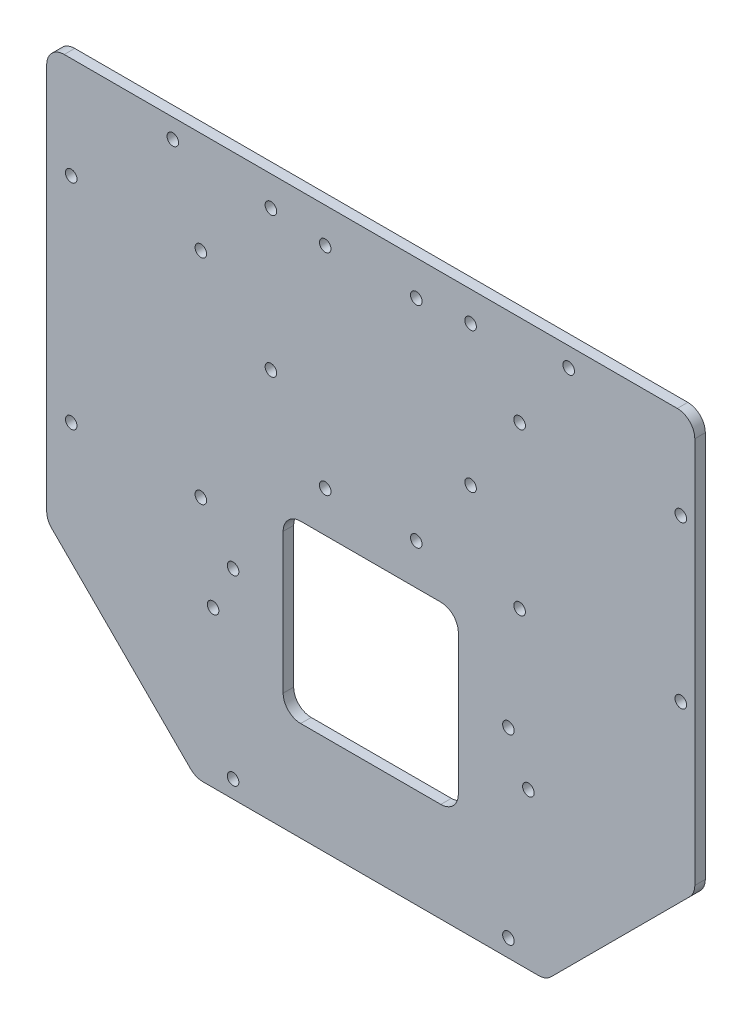
SolidWorks part; units mm, degrees
ref_plane "前视基准面" through (0, 0, 0) normal (0, 0, 1) x (1, 0, 0)
ref_plane "上视基准面" through (0, 0, 0) normal (0, 1, 0) x (1, 0, 0)
ref_plane "右视基准面" through (0, 0, 0) normal (1, 0, 0) x (0, 0, -1)
sketch "草图1" plane through (0, 0, 0) normal (0, 0, 1) x (1, 0, 0)
  line L1 (-87.5, 103.8596) -> (87.5, 103.8596)
  line L2 (-92.5, 98.8596) -> (-92.5, -13.6404)
  line L3 (-50, -56.1404) -> (50, -56.1404)
  line L4 (92.5, 98.8596) -> (92.5, -13.6404)
  line L5 (-92.5, 103.8596) -> (50, -56.1404) construction
  line L6 (-50, -56.1404) -> (92.5, 103.8596) construction
  line L7 (0, 103.8596) -> (0, -56.1404) construction
  line L9 (-92.5, -13.6404) -> (-50, -56.1404)
  line L10 (92.5, -13.6404) -> (50, -56.1404)
  arc A0 (87.5, 103.8596) -> (92.5, 98.8596) centre (87.5, 98.8596) cw
  arc A1 (-87.5, 103.8596) -> (-92.5, 98.8596) centre (-87.5, 98.8596) ccw
  point P0 (0, 0)
  dimension "D5" = 5
  dimension "D1" = 185
  dimension "D2" = 160
  dimension "D3" = 135
  dimension "D4" = 100
extrude "凸台-拉伸1" add sketch "草图1" along normal blind 3
sketch "草图2" plane through (0, 0, 3) normal (0, 0, 1) x (1, 0, 0)
  line L0 (87.5, 103.8596) -> (-87.5, 103.8596) construction
  line L1 (-28.5, 95.3596) -> (28.5, 95.3596) construction
  line L2 (-28.5, 95.3596) -> (-28.5, 55.3596) construction
  line L3 (-28.5, 55.3596) -> (28.5, 55.3596) construction
  line L4 (28.5, 95.3596) -> (28.5, 55.3596) construction
  line L5 (-28.5, 95.3596) -> (28.5, 55.3596) construction
  line L6 (-28.5, 55.3596) -> (28.5, 95.3596) construction
  line L7 (0, 0) -> (0, 75.3596) construction
  circle A0 centre (-28.5, 95.3596) radius 1.65
  circle A1 centre (28.5, 95.3596) radius 1.65
  circle A2 centre (-28.5, 55.3596) radius 1.65
  circle A3 centre (28.5, 55.3596) radius 1.65
  point P0 (0, 75.3596)
  dimension "D4" = 3.3
  dimension "D1" = 28.5
  dimension "D2" = 57
  dimension "D3" = 40
extrude "切除-拉伸1" cut sketch "草图2" against normal blind 10
sketch "草图3" plane through (0, 0, 3) normal (0, 0, 1) x (1, 0, 0)
  line L0 (-92.5, 98.8596) -> (-92.5, -13.6404) construction
  line L1 (-85.5, 74.8596) -> (-48.5, 74.8596) construction
  line L2 (-85.5, 74.8596) -> (-85.5, 13.8596) construction
  line L3 (-85.5, 13.8596) -> (-48.5, 13.8596) construction
  line L4 (-48.5, 74.8596) -> (-48.5, 13.8596) construction
  line L5 (-50, -56.1404) -> (50, -56.1404) construction
  circle A0 centre (-85.5, 74.8596) radius 1.65
  circle A1 centre (-48.5, 74.8596) radius 1.65
  circle A2 centre (-85.5, 13.8596) radius 1.65
  circle A3 centre (-48.5, 13.8596) radius 1.65
  dimension "D5" = 3.3
  dimension "D1" = 61
  dimension "D2" = 37
  dimension "D3" = 7
  dimension "D4" = 70
extrude "切除-拉伸2" cut sketch "草图3" against normal blind 10
sketch "草图4" plane through (0, 0, 3) normal (0, 0, 1) x (1, 0, 0)
  line L0 (92.5, -13.6404) -> (92.5, 98.8596) construction
  line L1 (42.5, 77.8596) -> (88.5, 77.8596) construction
  line L2 (42.5, 77.8596) -> (42.5, 31.8596) construction
  line L3 (42.5, 31.8596) -> (88.5, 31.8596) construction
  line L4 (88.5, 77.8596) -> (88.5, 31.8596) construction
  line L5 (87.5, 103.8596) -> (-87.5, 103.8596) construction
  circle A0 centre (42.5, 77.8596) radius 1.65
  circle A1 centre (88.5, 77.8596) radius 1.65
  circle A2 centre (42.5, 31.8596) radius 1.65
  circle A3 centre (88.5, 31.8596) radius 1.65
  dimension "D5" = 3.3
  dimension "D1" = 46
  dimension "D2" = 46
  dimension "D3" = 4
  dimension "D4" = 26
extrude "切除-拉伸3" cut sketch "草图4" against normal blind 10
sketch "草图5" plane through (0, 0, 3) normal (0, 0, 1) x (1, 0, 0)
  line L0 (-50, -56.1404) -> (50, -56.1404) construction
  line L1 (-39.3, 0.8596) -> (39.3, 0.8596) construction
  line L2 (-39.3, 0.8596) -> (-39.3, -51.1404) construction
  line L3 (-39.3, -51.1404) -> (39.3, -51.1404) construction
  line L4 (39.3, 0.8596) -> (39.3, -51.1404) construction
  line L5 (0, -56.1404) -> (0, 103.8596) construction
  line L6 (87.5, 103.8596) -> (-87.5, 103.8596) construction
  circle A0 centre (-39.3, 0.8596) radius 1.65
  circle A1 centre (39.3, 0.8596) radius 1.65
  circle A2 centre (-39.3, -51.1404) radius 1.65
  circle A3 centre (39.3, -51.1404) radius 1.65
  dimension "D4" = 3.3
  dimension "D1" = 78.6
  dimension "D2" = 52
  dimension "D3" = 5
extrude "切除-拉伸4" cut sketch "草图5" against normal blind 10
sketch "草图6" plane through (0, 0, 3) normal (0, 0, 1) x (1, 0, 0)
  line L0 (87.5, 103.8596) -> (-87.5, 103.8596) construction
  line L1 (-56.5, 98.3596) -> (56.5, 98.3596) construction
  line L2 (-56.5, 98.3596) -> (-56.5, -11.6404) construction
  line L3 (-56.5, -11.6404) -> (56.5, -11.6404) construction
  line L4 (56.5, 98.3596) -> (56.5, -11.6404) construction
  line L7 (0, -56.1404) -> (0, 98.3596) construction
  line L8 (-50, -56.1404) -> (50, -56.1404) construction
  circle A0 centre (-56.5, 98.3596) radius 1.65
  circle A1 centre (56.5, 98.3596) radius 1.65
  circle A4 centre (-45, -11.6404) radius 1.65
  circle A5 centre (45, -11.6404) radius 1.65
  dimension "D5" = 3.3
  dimension "D7" = 3.3
  dimension "D1" = 5.5
  dimension "D2" = 113
  dimension "D3" = 110
  dimension "D6" = 90
extrude "切除-拉伸5" cut sketch "草图6" against normal blind 10
sketch "草图7" plane through (0, 0, 3) normal (0, 0, 1) x (1, 0, 0)
  line L0 (0, 0) -> (0, 63.8596) construction
  line L1 (-13, 33.8596) -> (13, 33.8596) construction
  line L2 (-13, 33.8596) -> (-13, 93.8596) construction
  line L3 (-13, 93.8596) -> (13, 93.8596) construction
  line L4 (13, 33.8596) -> (13, 93.8596) construction
  line L5 (-13, 33.8596) -> (13, 93.8596) construction
  line L6 (-13, 93.8596) -> (13, 33.8596) construction
  line L8 (87.5, 103.8596) -> (-87.5, 103.8596) construction
  circle A0 centre (-13, 93.8596) radius 1.65
  circle A1 centre (13, 93.8596) radius 1.65
  circle A2 centre (13, 33.8596) radius 1.65
  circle A3 centre (-13, 33.8596) radius 1.65
  point P0 (0, 63.8596)
  dimension "D1" = 3.3
  dimension "D2" = 26
  dimension "D3" = 60
  dimension "D4" = 10
extrude "切除-拉伸6" cut sketch "草图7" against normal blind 10
sketch "草图8" plane through (0, 0, 3) normal (0, 0, 1) x (1, 0, 0)
  line L0 (0, 0) -> (0, 71.5605) construction
  line L2 (-20, 22.2174) -> (20, 22.2174)
  line L3 (-25, 17.2174) -> (-25, -22.7826)
  line L4 (-20, -27.7826) -> (20, -27.7826)
  line L5 (25, 17.2174) -> (25, -22.7826)
  line L6 (-25, 22.2174) -> (25, -27.7826) construction
  line L7 (-25, -27.7826) -> (25, 22.2174) construction
  arc A0 (20, 22.2174) -> (25, 17.2174) centre (20, 17.2174) cw
  arc A1 (20, -27.7826) -> (25, -22.7826) centre (20, -22.7826) ccw
  arc A2 (-25, -22.7826) -> (-20, -27.7826) centre (-20, -22.7826) ccw
  arc A3 (-20, 22.2174) -> (-25, 17.2174) centre (-20, 17.2174) ccw
  point P3 (0, -2.7826)
  dimension "D1" = 5
  dimension "D2" = 50
  dimension "D3" = 50
extrude "切除-拉伸7" cut sketch "草图8" against normal blind 10
fillet "圆角1" radius 5 4 edges at (92.5, -13.6404, 1.5) (50, -56.1404, 1.5) (-50, -56.1404, 1.5) (-92.5, -13.6404, 1.5)
